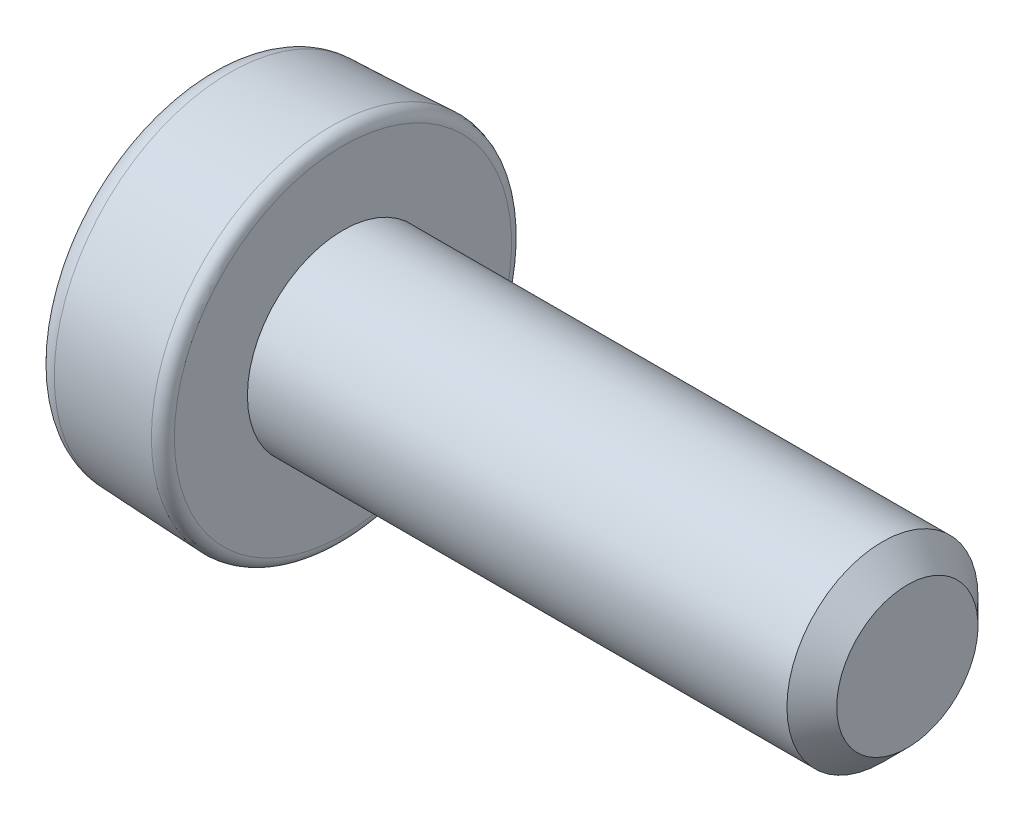
SolidWorks part; units mm, degrees
material "Acier allié inoxydable"
ref_plane "Plan de face" through (0, 0, 0) normal (0, 0, 1) x (1, 0, 0)
ref_plane "Plan de dessus" through (0, 0, 0) normal (0, 1, 0) x (1, 0, 0)
ref_plane "Plan de droite" through (0, 0, 0) normal (1, 0, 0) x (0, 0, -1)
sketch "Esquisse1" plane through (0, 0, 0) normal (0, 0, 1) x (1, 0, 0)
  line L0 (-2.7839, 0) -> (5.865, 0) construction
  line L1 (5.0216, 0) -> (5.0216, 0.6284)
  line L2 (5.0216, 0.6284) -> (4.8, 0.85)
  line L3 (4.8, 0.85) -> (0, 0.85)
  line L4 (0, 0.85) -> (0, 1.5001)
  line L5 (-0.1045, 1.6) -> (-1.009, 1.5592)
  line L6 (-1.2, 1.3594) -> (-1.2, 0)
  line L7 (-1.2, 0) -> (5.0216, 0)
  arc A0 (-1.2, 1.3594) -> (-1.009, 1.5592) centre (-1, 1.3594) cw
  arc A1 (-0.1045, 1.6) -> (0, 1.5001) centre (-0.1, 1.5001) cw
  dimension "D8" = 0.2
  dimension "D9" = 0.1
  dimension "D1" = 0.85
  dimension "D2" = 1.3594
  dimension "D3" = 4.8
  dimension "D4" = 1.6
  dimension "D5" = 1.2
  dimension "D6" = 135
revolve "Révolution1" add sketch "Esquisse1" angle 360 about L0
sketch "Esquisse2" plane through (-1.2, 0, 0) normal (-1, 0, 0) x (0, 0, 1)
  line L1 (-0.15, 0) -> (0.15, 0)
  line L2 (-0.15, 0) -> (-0.15, 0.8)
  line L3 (-0.15, 0.8) -> (0.15, 0.8)
  line L4 (0.15, 0) -> (0.15, 0.8)
  dimension "D1" = 0.3
  dimension "D2" = 0.8
extrude "Extrusion1" cut sketch "Esquisse2" against normal blind 0.3
pattern_circular "Répétition circulaire1" count 4 over 360 about axis through (0, 0, 0) along (1, 0, 0) of "Extrusion1"
chamfer "Chanfrein1" distance 0.2 angle 45 4 edges at (-1.05, 0.15, -0.15) (-1.05, -0.15, -0.15) (-1.05, 0.15, 0.15) (-1.05, -0.15, 0.15)
